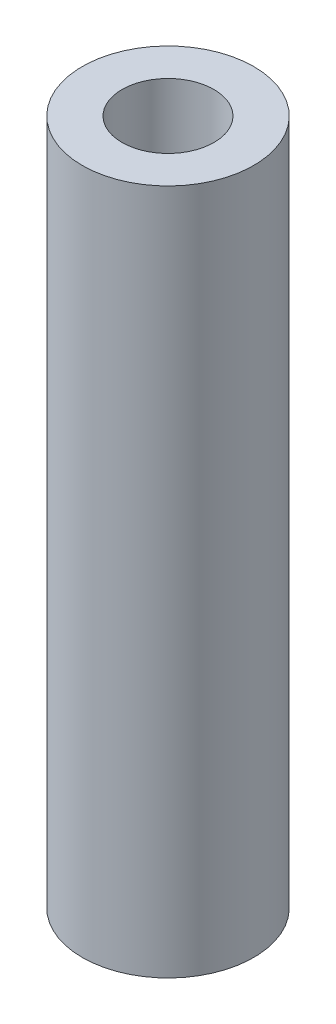
SolidWorks part; units mm, degrees
ref_plane "Front Plane" through (0, 0, 0) normal (0, 0, 1) x (1, 0, 0)
ref_plane "Top Plane" through (0, 0, 0) normal (0, 1, 0) x (1, 0, 0)
ref_plane "Right Plane" through (0, 0, 0) normal (1, 0, 0) x (0, 0, -1)
sketch "Sketch1" plane through (0, 0, 0) normal (0, 1, 0) x (1, 0, 0)
  circle A0 centre (0, 0) radius 3.175
  circle A1 centre (0, 0) radius 1.7018
  dimension "D1" = 3.4036
  dimension "D2" = 6.35
extrude "Extrude1" add sketch "Sketch1" along normal blind 25.4
